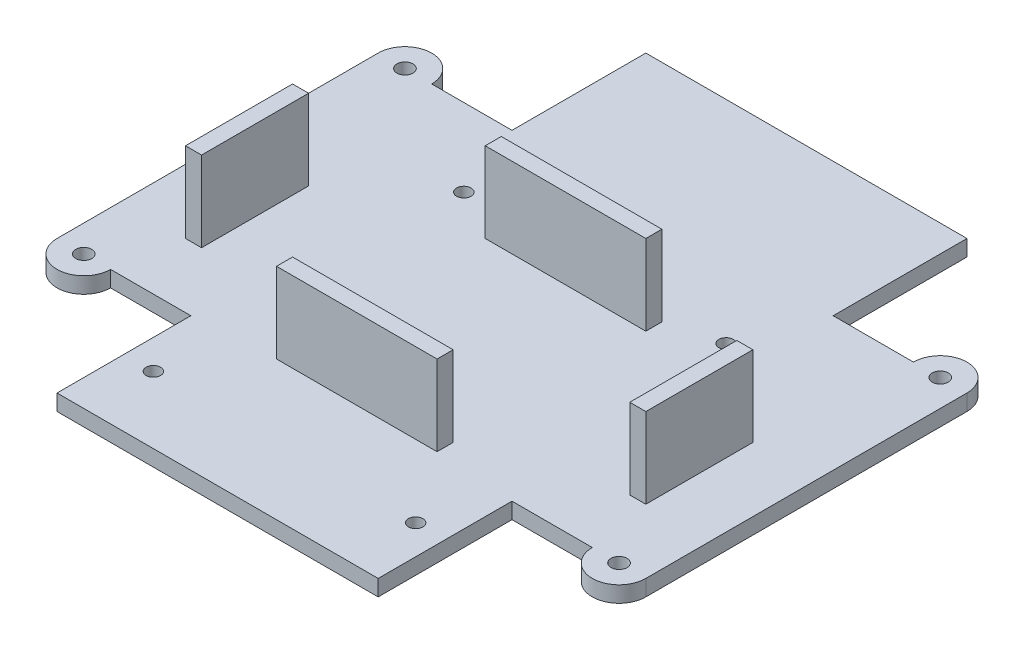
SolidWorks part; units mm, degrees
ref_plane "Front Plane" through (0, 0, 0) normal (0, 0, 1) x (1, 0, 0)
ref_plane "Top Plane" through (0, 0, 0) normal (0, 1, 0) x (1, 0, 0)
ref_plane "Right Plane" through (0, 0, 0) normal (1, 0, 0) x (0, 0, -1)
sketch "Sketch2" plane through (0, 0, 0) normal (0, 1, 0) x (1, 0, 0)
  line L0 (0, -55) -> (0, 55) construction
  line L1 (30, -55) -> (-30, -55)
  line L2 (55, -30) -> (55, 30)
  line L3 (30, 55) -> (-30, 55)
  line L4 (-55, -30) -> (-55, 30)
  line L5 (55, -55) -> (-55, 55) construction
  line L6 (55, 55) -> (-55, -55) construction
  line L7 (-55, 55) -> (-30, 55) construction
  line L8 (-55, 55) -> (-55, 30) construction
  line L9 (-55, 30) -> (-30, 30)
  line L10 (-30, 55) -> (-30, 30)
  line L11 (55, 30) -> (30, 30)
  line L12 (30, 55) -> (30, 30)
  line L13 (55, 55) -> (30, 55) construction
  line L14 (55, 55) -> (55, 30) construction
  line L15 (-55, 0) -> (55, 0) construction
  line L16 (55, -55) -> (30, -55) construction
  line L17 (30, -55) -> (30, -30)
  line L18 (55, -30) -> (30, -30)
  line L19 (55, -55) -> (55, -30) construction
  line L20 (-55, -30) -> (-30, -30)
  line L21 (-30, -55) -> (-30, -30)
  line L22 (-55, -55) -> (-30, -55) construction
  line L23 (-55, -55) -> (-55, -30) construction
  line L24 (-55, 30) -> (-55, 55) construction
  line L25 (-30, 55) -> (-55, 55) construction
  line L26 (55, 55) -> (30, 55) construction
  line L27 (55, 30) -> (55, 55) construction
  line L28 (55, -55) -> (55, -30) construction
  line L29 (55, -55) -> (30, -55) construction
  line L30 (-30, -55) -> (-55, -55) construction
  line L31 (-55, -55) -> (-55, -30) construction
  line L32 (0, 55) -> (0, -55) construction
  line L33 (28, -46) -> (-28, -46) construction
  line L34 (28, -46) -> (28, 44) construction
  line L35 (28, 44) -> (-28, 44) construction
  line L36 (-28, -46) -> (-28, 44) construction
  line L37 (28, -46) -> (-28, 44) construction
  line L38 (28, 44) -> (-28, -46) construction
  circle A0 centre (24.5, -42.5) radius 1.35
  circle A1 centre (-24.5, -42.5) radius 1.35
  circle A2 centre (24.5, 15.5) radius 1.35
  circle A3 centre (-24.5, 15.5) radius 1.35
  point P0 (0, 0)
  point P22 (0, -1)
  dimension "D7" = 2.7
  dimension "D10" = 2.7
  dimension "D15" = 2.7
  dimension "D16" = 2.7
  dimension "D1" = 25
  dimension "D2" = 25
  dimension "D3" = 60
  dimension "D4" = 56
  dimension "D5" = 90
  dimension "D6" = 9
  dimension "D8" = 3.5
  dimension "D9" = 3.5
  dimension "D11" = 3.5
  dimension "D12" = 3.5
  dimension "D13" = 61.5
  dimension "D14" = 3.5
  dimension "D17" = 3.5
  dimension "D18" = 61.5
extrude "Boss-Extrude1" add sketch "Sketch2" along normal blind 3
sketch "Sketch3" plane through (0, 3, 0) normal (0, 1, 0) x (1, 0, 0)
  line L1 (55, -30) -> (55, 30) construction
  line L2 (55, 30) -> (30, 30) construction
  line L3 (-55, 0) -> (55, 0) construction
  line L4 (0, -55) -> (0, 55) construction
  circle A0 centre (50, 30) radius 5
  circle A4 centre (50, -30) radius 5
  circle A5 centre (-50, -30) radius 5
  circle A6 centre (-50, 30) radius 5
  point P3 (-31.3322, 28.0303)
  point P4 (30, 30)
  point P5 (0, 0)
  point P8 (50, 30)
  dimension "D1" = 10
extrude "Boss-Extrude2" add sketch "Sketch3" against normal up to surface (3 mm away) up to face at (0, 0, 0)
sketch "Sketch4" plane through (0, 3, 0) normal (0, 1, 0) x (1, 0, 0)
  line L0 (-55, 0) -> (55, 0) construction
  line L1 (0, -55) -> (0, 55) construction
  circle A0 centre (50, 30) radius 1.5
  circle A4 centre (50, -30) radius 1.5
  circle A5 centre (-50, -30) radius 1.5
  circle A6 centre (-50, 30) radius 1.5
  dimension "D1" = 3
extrude "Cut-Extrude1" cut sketch "Sketch4" against normal through all
sketch "Sketch5" plane through (0, 3, 0) normal (0, 1, 0) x (1, 0, 0)
  line L0 (0, 55) -> (0, -55) construction
  line L1 (30, 55) -> (-30, 55) construction
  line L2 (-30, -55) -> (30, -55) construction
  line L3 (30, -30) -> (45, -30) construction
  line L4 (-40, -26) -> (40, -26) construction
  line L5 (-40, -26) -> (-40, 10) construction
  line L6 (-40, 10) -> (40, 10) construction
  line L7 (40, -26) -> (40, 10) construction
  line L8 (-40, -26) -> (40, 10) construction
  line L9 (-40, 10) -> (40, -26) construction
  line L10 (-43, -29) -> (-43, 13) construction
  line L11 (-43, 13) -> (43, 13) construction
  line L12 (43, -29) -> (43, 13) construction
  line L13 (-43, -29) -> (43, -29) construction
  line L14 (-43, 2) -> (-40, 2)
  line L15 (-43, -18) -> (-40, -18)
  line L16 (-43, -8) -> (43, -8) construction
  line L17 (43, -18) -> (40, -18)
  line L18 (43, 2) -> (40, 2)
  line L19 (-15, 13) -> (-15, 10)
  line L20 (15, 13) -> (15, 10)
  line L21 (-43, 2) -> (-43, -18)
  line L22 (-40, 2) -> (-40, -18)
  line L23 (-15, 13) -> (15, 13)
  line L24 (15, 10) -> (-15, 10)
  line L25 (40, 2) -> (40, -18)
  line L26 (43, 2) -> (43, -18)
  line L27 (15, -29) -> (15, -26)
  line L28 (-15, -29) -> (15, -29)
  line L29 (-15, -29) -> (-15, -26)
  line L30 (15, -26) -> (-15, -26)
  point P6 (0, -8)
  dimension "D1" = 80
  dimension "D2" = 36
  dimension "D3" = 4
  dimension "D5" = 10
  dimension "D6" = 10
  dimension "D7" = 15
  dimension "D8" = 15
  dimension "D4" = 3
extrude "Boss-Extrude3" add sketch "Sketch5" along normal blind 15
